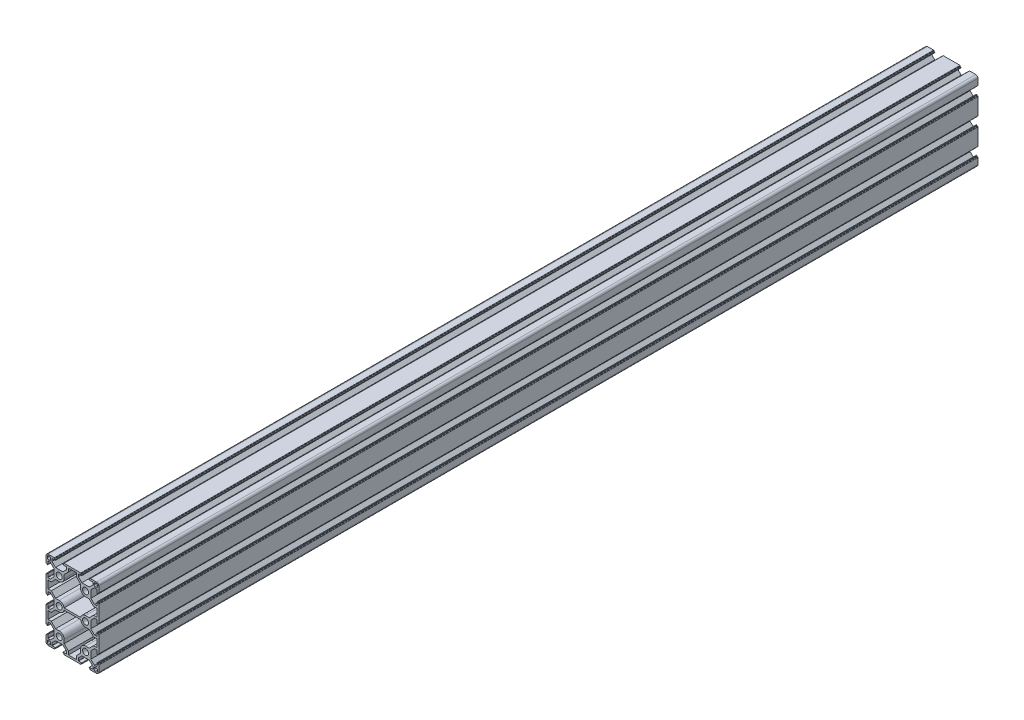
SolidWorks part; units mm, degrees
material "6063 T5"
ref_plane "Спереди" through (0, 0, 0) normal (0, 0, 1) x (1, 0, 0)
ref_plane "Сверху" through (0, 0, 0) normal (0, 1, 0) x (1, 0, 0)
ref_plane "Справа" through (0, 0, 0) normal (1, 0, 0) x (0, 0, -1)
sketch "Эскиз1" plane through (0, 0, 0) normal (0, 0, 1) x (1, 0, 0)
  line L0 (-34.4622, 45.0307) -> (-34.4622, -44.9693) construction
  line L1 (0, 45) -> (0, -45) construction
  line L2 (30, 0) -> (-30, 0) construction
  line L3 (-30, 38.25) -> (-30, 42.5)
  line L4 (-27.5, 45) -> (-23.25, 45)
  line L5 (4.5, 42.8) -> (-4.5, 42.8)
  line L6 (-27.35, 43.55) -> (-25.95, 43.55)
  line L7 (-28.55, 42.35) -> (-28.55, 40.95)
  line L8 (-27.35, 39.75) -> (-25.95, 39.75)
  line L9 (-24.75, 42.35) -> (-24.75, 40.95)
  line L10 (-4.5, 42.8) -> (-4.5, 38.9059)
  line L11 (-4.5, 38.9059) -> (-9.3, 34.1059)
  line L12 (-9.3, 34.1059) -> (-9.3, 30)
  line L13 (-15, 24.3) -> (-19.1059, 24.3)
  line L14 (-19.1059, 24.3) -> (-24.0559, 19.35)
  line L15 (-24.0559, 19.35) -> (-27.8, 19.35)
  line L16 (-27.8, 19.35) -> (-27.8, 10.65)
  line L17 (-27.8, 10.65) -> (-24.0559, 10.65)
  line L18 (-24.0559, 10.65) -> (-19.1059, 5.7)
  line L19 (-19.1059, 5.7) -> (-15, 5.7)
  line L20 (-9.4071, 1.1) -> (9.4071, 1.1)
  line L21 (-6.75, 45) -> (6.75, 45)
  line L22 (-30, 21.75) -> (-30, 8.25)
  line L23 (30, 21.75) -> (30, 8.25)
  line L24 (27.5, 45) -> (23.25, 45)
  line L25 (30, 38.25) -> (30, 42.5)
  line L26 (19.1059, 5.7) -> (15, 5.7)
  line L27 (24.0559, 10.65) -> (19.1059, 5.7)
  line L28 (27.8, 10.65) -> (24.0559, 10.65)
  line L29 (27.8, 19.35) -> (27.8, 10.65)
  line L30 (24.0559, 19.35) -> (27.8, 19.35)
  line L31 (19.1059, 24.3) -> (24.0559, 19.35)
  line L32 (15, 24.3) -> (19.1059, 24.3)
  line L33 (9.3, 34.1059) -> (9.3, 30)
  line L34 (4.5, 38.9059) -> (9.3, 34.1059)
  line L35 (4.5, 42.8) -> (4.5, 38.9059)
  line L36 (27.35, 43.55) -> (25.95, 43.55)
  line L37 (28.55, 42.35) -> (28.55, 40.95)
  line L38 (27.35, 39.75) -> (25.95, 39.75)
  line L39 (24.75, 42.35) -> (24.75, 40.95)
  line L40 (27.5, -45) -> (23.25, -45)
  line L41 (30, -38.25) -> (30, -42.5)
  line L42 (27.35, -43.55) -> (25.95, -43.55)
  line L43 (24.75, -42.35) -> (24.75, -40.95)
  line L44 (27.35, -39.75) -> (25.95, -39.75)
  line L45 (28.55, -42.35) -> (28.55, -40.95)
  line L46 (30, -21.75) -> (30, -8.25)
  line L47 (-30, -21.75) -> (-30, -8.25)
  line L48 (-6.75, -45) -> (6.75, -45)
  line L49 (-4.5, -42.8) -> (-4.5, -38.9059)
  line L50 (4.5, -42.8) -> (-4.5, -42.8)
  line L51 (4.5, -42.8) -> (4.5, -38.9059)
  line L52 (4.5, -38.9059) -> (9.3, -34.1059)
  line L53 (9.3, -34.1059) -> (9.3, -30)
  line L54 (15, -24.3) -> (19.1059, -24.3)
  line L55 (19.1059, -24.3) -> (24.0559, -19.35)
  line L56 (24.0559, -19.35) -> (27.8, -19.35)
  line L57 (27.8, -19.35) -> (27.8, -10.65)
  line L58 (27.8, -10.65) -> (24.0559, -10.65)
  line L59 (24.0559, -10.65) -> (19.1059, -5.7)
  line L60 (19.1059, -5.7) -> (15, -5.7)
  line L61 (-9.4071, -1.1) -> (9.4071, -1.1)
  line L62 (-19.1059, -5.7) -> (-15, -5.7)
  line L63 (-24.0559, -10.65) -> (-19.1059, -5.7)
  line L64 (-27.8, -10.65) -> (-24.0559, -10.65)
  line L65 (-27.8, -19.35) -> (-27.8, -10.65)
  line L66 (-24.0559, -19.35) -> (-27.8, -19.35)
  line L67 (-19.1059, -24.3) -> (-24.0559, -19.35)
  line L68 (-15, -24.3) -> (-19.1059, -24.3)
  line L69 (-9.3, -34.1059) -> (-9.3, -30)
  line L70 (-4.5, -38.9059) -> (-9.3, -34.1059)
  line L71 (-27.35, -43.55) -> (-25.95, -43.55)
  line L72 (-28.55, -42.35) -> (-28.55, -40.95)
  line L73 (-27.35, -39.75) -> (-25.95, -39.75)
  line L74 (-24.75, -42.35) -> (-24.75, -40.95)
  line L75 (-27.5, -45) -> (-23.25, -45)
  line L76 (-30, -38.25) -> (-30, -42.5)
  arc A0 (-30, 42.5) -> (-27.5, 45) centre (-27.5, 42.5) cw
  arc A1 (-28.55, 40.95) -> (-27.35, 39.75) centre (-27.35, 40.95) ccw
  arc A2 (-25.95, 39.75) -> (-24.75, 40.95) centre (-25.95, 40.95) ccw
  arc A3 (-25.95, 43.55) -> (-24.75, 42.35) centre (-25.95, 42.35) cw
  arc A4 (-27.35, 43.55) -> (-28.55, 42.35) centre (-27.35, 42.35) ccw
  circle A5 centre (-15, 30) radius 3.4
  arc A6 (-9.3, 30) -> (-15, 24.3) centre (-15, 30) cw
  arc A7 (-15, 5.7) -> (-9.4071, 1.1) centre (-15, 0) cw
  circle A8 centre (-15, 0) radius 3.4
  arc A9 (30, 42.5) -> (27.5, 45) centre (27.5, 42.5) ccw
  arc A10 (15, 5.7) -> (9.4071, 1.1) centre (15, 0) ccw
  arc A11 (9.3, 30) -> (15, 24.3) centre (15, 30) ccw
  circle A12 centre (15, 30) radius 3.4
  circle A13 centre (15, 0) radius 3.4
  arc A14 (25.95, 43.55) -> (24.75, 42.35) centre (25.95, 42.35) ccw
  arc A15 (27.35, 43.55) -> (28.55, 42.35) centre (27.35, 42.35) cw
  arc A16 (28.55, 40.95) -> (27.35, 39.75) centre (27.35, 40.95) cw
  arc A17 (25.95, 39.75) -> (24.75, 40.95) centre (25.95, 40.95) cw
  arc A18 (30, -42.5) -> (27.5, -45) centre (27.5, -42.5) cw
  arc A19 (27.35, -43.55) -> (28.55, -42.35) centre (27.35, -42.35) ccw
  arc A20 (25.95, -43.55) -> (24.75, -42.35) centre (25.95, -42.35) cw
  arc A21 (25.95, -39.75) -> (24.75, -40.95) centre (25.95, -40.95) ccw
  arc A22 (28.55, -40.95) -> (27.35, -39.75) centre (27.35, -40.95) ccw
  circle A23 centre (-15, -30) radius 3.4
  circle A24 centre (15, -30) radius 3.4
  arc A25 (9.3, -30) -> (15, -24.3) centre (15, -30) cw
  arc A26 (15, -5.7) -> (9.4071, -1.1) centre (15, 0) cw
  arc A27 (-15, -5.7) -> (-9.4071, -1.1) centre (-15, 0) ccw
  arc A28 (-9.3, -30) -> (-15, -24.3) centre (-15, -30) ccw
  arc A29 (-25.95, -43.55) -> (-24.75, -42.35) centre (-25.95, -42.35) ccw
  arc A30 (-27.35, -43.55) -> (-28.55, -42.35) centre (-27.35, -42.35) cw
  arc A31 (-28.55, -40.95) -> (-27.35, -39.75) centre (-27.35, -40.95) cw
  arc A32 (-25.95, -39.75) -> (-24.75, -40.95) centre (-25.95, -40.95) cw
  arc A33 (-30, -42.5) -> (-27.5, -45) centre (-27.5, -42.5) ccw
  point P22 (-24.75, 43.55)
  point P25 (-28.55, 43.55)
  point P63 (0, 1.1)
  point P72 (0, 42.8)
  line B0 (-30, 8.25) -> (-30, 5.5)
  line B1 (-29.7, 5.2) -> (-29.3, 5.2)
  line B2 (-29, 4.9) -> (-29, 4.4)
  line B3 (-28.7, 4.1) -> (-28.3, 4.1)
  line B4 (-28, 4.4) -> (-28, 7.95)
  line B5 (-27.7, 8.25) -> (-25.05, 8.25)
  line B6 (-25.05, 8.25) -> (-21, 4.2)
  line B7 (-21, 0) -> (-30, 0) construction
  line B8 (-21, -4.2) -> (-21, 4.2)
  line B9 (-25.05, -8.25) -> (-21, -4.2)
  line B10 (-27.7, -8.25) -> (-25.05, -8.25)
  line B11 (-28, -4.4) -> (-28, -7.95)
  line B12 (-28.7, -4.1) -> (-28.3, -4.1)
  line B13 (-29, -4.9) -> (-29, -4.4)
  line B14 (-29.7, -5.2) -> (-29.3, -5.2)
  line B15 (-30, -8.25) -> (-30, -5.5)
  arc B16 (-28, 7.95) -> (-27.7, 8.25) centre (-27.7, 7.95) cw
  arc B17 (-28.3, 4.1) -> (-28, 4.4) centre (-28.3, 4.4) ccw
  arc B18 (-29, 4.4) -> (-28.7, 4.1) centre (-28.7, 4.4) ccw
  arc B19 (-29.3, 5.2) -> (-29, 4.9) centre (-29.3, 4.9) cw
  arc B20 (-30, 5.5) -> (-29.7, 5.2) centre (-29.7, 5.5) ccw
  arc B21 (-30, -5.5) -> (-29.7, -5.2) centre (-29.7, -5.5) cw
  arc B22 (-29.3, -5.2) -> (-29, -4.9) centre (-29.3, -4.9) ccw
  arc B23 (-29, -4.4) -> (-28.7, -4.1) centre (-28.7, -4.4) cw
  arc B24 (-28.3, -4.1) -> (-28, -4.4) centre (-28.3, -4.4) cw
  arc B25 (-28, -7.95) -> (-27.7, -8.25) centre (-27.7, -7.95) ccw
  line B26 (-30, 38.25) -> (-30, 35.5)
  line B27 (-29.7, 35.2) -> (-29.3, 35.2)
  line B28 (-29, 34.9) -> (-29, 34.4)
  line B29 (-28.7, 34.1) -> (-28.3, 34.1)
  line B30 (-28, 34.4) -> (-28, 37.95)
  line B31 (-27.7, 38.25) -> (-25.05, 38.25)
  line B32 (-25.05, 38.25) -> (-21, 34.2)
  line B33 (-21, 30) -> (-30, 30) construction
  line B34 (-21, 25.8) -> (-21, 34.2)
  line B35 (-25.05, 21.75) -> (-21, 25.8)
  line B36 (-27.7, 21.75) -> (-25.05, 21.75)
  line B37 (-28, 25.6) -> (-28, 22.05)
  line B38 (-28.7, 25.9) -> (-28.3, 25.9)
  line B39 (-29, 25.1) -> (-29, 25.6)
  line B40 (-29.7, 24.8) -> (-29.3, 24.8)
  line B41 (-30, 21.75) -> (-30, 24.5)
  arc B42 (-28, 37.95) -> (-27.7, 38.25) centre (-27.7, 37.95) cw
  arc B43 (-28.3, 34.1) -> (-28, 34.4) centre (-28.3, 34.4) ccw
  arc B44 (-29, 34.4) -> (-28.7, 34.1) centre (-28.7, 34.4) ccw
  arc B45 (-29.3, 35.2) -> (-29, 34.9) centre (-29.3, 34.9) cw
  arc B46 (-30, 35.5) -> (-29.7, 35.2) centre (-29.7, 35.5) ccw
  arc B47 (-30, 24.5) -> (-29.7, 24.8) centre (-29.7, 24.5) cw
  arc B48 (-29.3, 24.8) -> (-29, 25.1) centre (-29.3, 25.1) ccw
  arc B49 (-29, 25.6) -> (-28.7, 25.9) centre (-28.7, 25.6) cw
  arc B50 (-28.3, 25.9) -> (-28, 25.6) centre (-28.3, 25.6) cw
  arc B51 (-28, 22.05) -> (-27.7, 21.75) centre (-27.7, 22.05) ccw
  line B52 (-6.75, 45) -> (-9.5, 45)
  line B53 (-9.8, 44.7) -> (-9.8, 44.3)
  line B54 (-10.1, 44) -> (-10.6, 44)
  line B55 (-10.9, 43.7) -> (-10.9, 43.3)
  line B56 (-10.6, 43) -> (-7.05, 43)
  line B57 (-6.75, 42.7) -> (-6.75, 40.05)
  line B58 (-6.75, 40.05) -> (-10.8, 36)
  line B59 (-15, 36) -> (-15, 45) construction
  line B60 (-19.2, 36) -> (-10.8, 36)
  line B61 (-23.25, 40.05) -> (-19.2, 36)
  line B62 (-23.25, 42.7) -> (-23.25, 40.05)
  line B63 (-19.4, 43) -> (-22.95, 43)
  line B64 (-19.1, 43.7) -> (-19.1, 43.3)
  line B65 (-19.9, 44) -> (-19.4, 44)
  line B66 (-20.2, 44.7) -> (-20.2, 44.3)
  line B67 (-23.25, 45) -> (-20.5, 45)
  arc B68 (-7.05, 43) -> (-6.75, 42.7) centre (-7.05, 42.7) cw
  arc B69 (-10.9, 43.3) -> (-10.6, 43) centre (-10.6, 43.3) ccw
  arc B70 (-10.6, 44) -> (-10.9, 43.7) centre (-10.6, 43.7) ccw
  arc B71 (-9.8, 44.3) -> (-10.1, 44) centre (-10.1, 44.3) cw
  arc B72 (-9.5, 45) -> (-9.8, 44.7) centre (-9.5, 44.7) ccw
  arc B73 (-20.5, 45) -> (-20.2, 44.7) centre (-20.5, 44.7) cw
  arc B74 (-20.2, 44.3) -> (-19.9, 44) centre (-19.9, 44.3) ccw
  arc B75 (-19.4, 44) -> (-19.1, 43.7) centre (-19.4, 43.7) cw
  arc B76 (-19.1, 43.3) -> (-19.4, 43) centre (-19.4, 43.3) cw
  arc B77 (-22.95, 43) -> (-23.25, 42.7) centre (-22.95, 42.7) ccw
  line B78 (6.75, 45) -> (9.5, 45)
  line B79 (9.8, 44.7) -> (9.8, 44.3)
  line B80 (10.1, 44) -> (10.6, 44)
  line B81 (10.9, 43.7) -> (10.9, 43.3)
  line B82 (10.6, 43) -> (7.05, 43)
  line B83 (6.75, 42.7) -> (6.75, 40.05)
  line B84 (6.75, 40.05) -> (10.8, 36)
  line B85 (15, 36) -> (15, 45) construction
  line B86 (19.2, 36) -> (10.8, 36)
  line B87 (23.25, 40.05) -> (19.2, 36)
  line B88 (23.25, 42.7) -> (23.25, 40.05)
  line B89 (19.4, 43) -> (22.95, 43)
  line B90 (19.1, 43.7) -> (19.1, 43.3)
  line B91 (19.9, 44) -> (19.4, 44)
  line B92 (20.2, 44.7) -> (20.2, 44.3)
  line B93 (23.25, 45) -> (20.5, 45)
  arc B94 (7.05, 43) -> (6.75, 42.7) centre (7.05, 42.7) ccw
  arc B95 (10.9, 43.3) -> (10.6, 43) centre (10.6, 43.3) cw
  arc B96 (10.6, 44) -> (10.9, 43.7) centre (10.6, 43.7) cw
  arc B97 (9.8, 44.3) -> (10.1, 44) centre (10.1, 44.3) ccw
  arc B98 (9.5, 45) -> (9.8, 44.7) centre (9.5, 44.7) cw
  arc B99 (20.5, 45) -> (20.2, 44.7) centre (20.5, 44.7) ccw
  arc B100 (20.2, 44.3) -> (19.9, 44) centre (19.9, 44.3) cw
  arc B101 (19.4, 44) -> (19.1, 43.7) centre (19.4, 43.7) ccw
  arc B102 (19.1, 43.3) -> (19.4, 43) centre (19.4, 43.3) ccw
  arc B103 (22.95, 43) -> (23.25, 42.7) centre (22.95, 42.7) cw
  line B104 (30, 38.25) -> (30, 35.5)
  line B105 (29.7, 35.2) -> (29.3, 35.2)
  line B106 (29, 34.9) -> (29, 34.4)
  line B107 (28.7, 34.1) -> (28.3, 34.1)
  line B108 (28, 34.4) -> (28, 37.95)
  line B109 (27.7, 38.25) -> (25.05, 38.25)
  line B110 (25.05, 38.25) -> (21, 34.2)
  line B111 (21, 30) -> (30, 30) construction
  line B112 (21, 25.8) -> (21, 34.2)
  line B113 (25.05, 21.75) -> (21, 25.8)
  line B114 (27.7, 21.75) -> (25.05, 21.75)
  line B115 (28, 25.6) -> (28, 22.05)
  line B116 (28.7, 25.9) -> (28.3, 25.9)
  line B117 (29, 25.1) -> (29, 25.6)
  line B118 (29.7, 24.8) -> (29.3, 24.8)
  line B119 (30, 21.75) -> (30, 24.5)
  arc B120 (28, 37.95) -> (27.7, 38.25) centre (27.7, 37.95) ccw
  arc B121 (28.3, 34.1) -> (28, 34.4) centre (28.3, 34.4) cw
  arc B122 (29, 34.4) -> (28.7, 34.1) centre (28.7, 34.4) cw
  arc B123 (29.3, 35.2) -> (29, 34.9) centre (29.3, 34.9) ccw
  arc B124 (30, 35.5) -> (29.7, 35.2) centre (29.7, 35.5) cw
  arc B125 (30, 24.5) -> (29.7, 24.8) centre (29.7, 24.5) ccw
  arc B126 (29.3, 24.8) -> (29, 25.1) centre (29.3, 25.1) cw
  arc B127 (29, 25.6) -> (28.7, 25.9) centre (28.7, 25.6) ccw
  arc B128 (28.3, 25.9) -> (28, 25.6) centre (28.3, 25.6) ccw
  arc B129 (28, 22.05) -> (27.7, 21.75) centre (27.7, 22.05) cw
  line B130 (30, 8.25) -> (30, 5.5)
  line B131 (29.7, 5.2) -> (29.3, 5.2)
  line B132 (29, 4.9) -> (29, 4.4)
  line B133 (28.7, 4.1) -> (28.3, 4.1)
  line B134 (28, 4.4) -> (28, 7.95)
  line B135 (27.7, 8.25) -> (25.05, 8.25)
  line B136 (25.05, 8.25) -> (21, 4.2)
  line B137 (21, 0) -> (30, 0) construction
  line B138 (21, -4.2) -> (21, 4.2)
  line B139 (25.05, -8.25) -> (21, -4.2)
  line B140 (27.7, -8.25) -> (25.05, -8.25)
  line B141 (28, -4.4) -> (28, -7.95)
  line B142 (28.7, -4.1) -> (28.3, -4.1)
  line B143 (29, -4.9) -> (29, -4.4)
  line B144 (29.7, -5.2) -> (29.3, -5.2)
  line B145 (30, -8.25) -> (30, -5.5)
  arc B146 (28, 7.95) -> (27.7, 8.25) centre (27.7, 7.95) ccw
  arc B147 (28.3, 4.1) -> (28, 4.4) centre (28.3, 4.4) cw
  arc B148 (29, 4.4) -> (28.7, 4.1) centre (28.7, 4.4) cw
  arc B149 (29.3, 5.2) -> (29, 4.9) centre (29.3, 4.9) ccw
  arc B150 (30, 5.5) -> (29.7, 5.2) centre (29.7, 5.5) cw
  arc B151 (30, -5.5) -> (29.7, -5.2) centre (29.7, -5.5) ccw
  arc B152 (29.3, -5.2) -> (29, -4.9) centre (29.3, -4.9) cw
  arc B153 (29, -4.4) -> (28.7, -4.1) centre (28.7, -4.4) ccw
  arc B154 (28.3, -4.1) -> (28, -4.4) centre (28.3, -4.4) ccw
  arc B155 (28, -7.95) -> (27.7, -8.25) centre (27.7, -7.95) cw
  line B156 (-6.75, -45) -> (-9.5, -45)
  line B157 (-9.8, -44.7) -> (-9.8, -44.3)
  line B158 (-10.1, -44) -> (-10.6, -44)
  line B159 (-10.9, -43.7) -> (-10.9, -43.3)
  line B160 (-10.6, -43) -> (-7.05, -43)
  line B161 (-6.75, -42.7) -> (-6.75, -40.05)
  line B162 (-6.75, -40.05) -> (-10.8, -36)
  line B163 (-15, -36) -> (-15, -45) construction
  line B164 (-19.2, -36) -> (-10.8, -36)
  line B165 (-23.25, -40.05) -> (-19.2, -36)
  line B166 (-23.25, -42.7) -> (-23.25, -40.05)
  line B167 (-19.4, -43) -> (-22.95, -43)
  line B168 (-19.1, -43.7) -> (-19.1, -43.3)
  line B169 (-19.9, -44) -> (-19.4, -44)
  line B170 (-20.2, -44.7) -> (-20.2, -44.3)
  line B171 (-23.25, -45) -> (-20.5, -45)
  arc B172 (-7.05, -43) -> (-6.75, -42.7) centre (-7.05, -42.7) ccw
  arc B173 (-10.9, -43.3) -> (-10.6, -43) centre (-10.6, -43.3) cw
  arc B174 (-10.6, -44) -> (-10.9, -43.7) centre (-10.6, -43.7) cw
  arc B175 (-9.8, -44.3) -> (-10.1, -44) centre (-10.1, -44.3) ccw
  arc B176 (-9.5, -45) -> (-9.8, -44.7) centre (-9.5, -44.7) cw
  arc B177 (-20.5, -45) -> (-20.2, -44.7) centre (-20.5, -44.7) ccw
  arc B178 (-20.2, -44.3) -> (-19.9, -44) centre (-19.9, -44.3) cw
  arc B179 (-19.4, -44) -> (-19.1, -43.7) centre (-19.4, -43.7) ccw
  arc B180 (-19.1, -43.3) -> (-19.4, -43) centre (-19.4, -43.3) ccw
  arc B181 (-22.95, -43) -> (-23.25, -42.7) centre (-22.95, -42.7) cw
  line B182 (-30, -38.25) -> (-30, -35.5)
  line B183 (-29.7, -35.2) -> (-29.3, -35.2)
  line B184 (-29, -34.9) -> (-29, -34.4)
  line B185 (-28.7, -34.1) -> (-28.3, -34.1)
  line B186 (-28, -34.4) -> (-28, -37.95)
  line B187 (-27.7, -38.25) -> (-25.05, -38.25)
  line B188 (-25.05, -38.25) -> (-21, -34.2)
  line B189 (-21, -30) -> (-30, -30) construction
  line B190 (-21, -25.8) -> (-21, -34.2)
  line B191 (-25.05, -21.75) -> (-21, -25.8)
  line B192 (-27.7, -21.75) -> (-25.05, -21.75)
  line B193 (-28, -25.6) -> (-28, -22.05)
  line B194 (-28.7, -25.9) -> (-28.3, -25.9)
  line B195 (-29, -25.1) -> (-29, -25.6)
  line B196 (-29.7, -24.8) -> (-29.3, -24.8)
  line B197 (-30, -21.75) -> (-30, -24.5)
  arc B198 (-28, -37.95) -> (-27.7, -38.25) centre (-27.7, -37.95) ccw
  arc B199 (-28.3, -34.1) -> (-28, -34.4) centre (-28.3, -34.4) cw
  arc B200 (-29, -34.4) -> (-28.7, -34.1) centre (-28.7, -34.4) cw
  arc B201 (-29.3, -35.2) -> (-29, -34.9) centre (-29.3, -34.9) ccw
  arc B202 (-30, -35.5) -> (-29.7, -35.2) centre (-29.7, -35.5) cw
  arc B203 (-30, -24.5) -> (-29.7, -24.8) centre (-29.7, -24.5) ccw
  arc B204 (-29.3, -24.8) -> (-29, -25.1) centre (-29.3, -25.1) cw
  arc B205 (-29, -25.6) -> (-28.7, -25.9) centre (-28.7, -25.6) ccw
  arc B206 (-28.3, -25.9) -> (-28, -25.6) centre (-28.3, -25.6) ccw
  arc B207 (-28, -22.05) -> (-27.7, -21.75) centre (-27.7, -22.05) cw
  line B208 (30, -38.25) -> (30, -35.5)
  line B209 (29.7, -35.2) -> (29.3, -35.2)
  line B210 (29, -34.9) -> (29, -34.4)
  line B211 (28.7, -34.1) -> (28.3, -34.1)
  line B212 (28, -34.4) -> (28, -37.95)
  line B213 (27.7, -38.25) -> (25.05, -38.25)
  line B214 (25.05, -38.25) -> (21, -34.2)
  line B215 (21, -30) -> (30, -30) construction
  line B216 (21, -25.8) -> (21, -34.2)
  line B217 (25.05, -21.75) -> (21, -25.8)
  line B218 (27.7, -21.75) -> (25.05, -21.75)
  line B219 (28, -25.6) -> (28, -22.05)
  line B220 (28.7, -25.9) -> (28.3, -25.9)
  line B221 (29, -25.1) -> (29, -25.6)
  line B222 (29.7, -24.8) -> (29.3, -24.8)
  line B223 (30, -21.75) -> (30, -24.5)
  arc B224 (28, -37.95) -> (27.7, -38.25) centre (27.7, -37.95) cw
  arc B225 (28.3, -34.1) -> (28, -34.4) centre (28.3, -34.4) ccw
  arc B226 (29, -34.4) -> (28.7, -34.1) centre (28.7, -34.4) ccw
  arc B227 (29.3, -35.2) -> (29, -34.9) centre (29.3, -34.9) cw
  arc B228 (30, -35.5) -> (29.7, -35.2) centre (29.7, -35.5) ccw
  arc B229 (30, -24.5) -> (29.7, -24.8) centre (29.7, -24.5) cw
  arc B230 (29.3, -24.8) -> (29, -25.1) centre (29.3, -25.1) ccw
  arc B231 (29, -25.6) -> (28.7, -25.9) centre (28.7, -25.6) cw
  arc B232 (28.3, -25.9) -> (28, -25.6) centre (28.3, -25.6) cw
  arc B233 (28, -22.05) -> (27.7, -21.75) centre (27.7, -22.05) ccw
  line B234 (6.75, -45) -> (9.5, -45)
  line B235 (9.8, -44.7) -> (9.8, -44.3)
  line B236 (10.1, -44) -> (10.6, -44)
  line B237 (10.9, -43.7) -> (10.9, -43.3)
  line B238 (10.6, -43) -> (7.05, -43)
  line B239 (6.75, -42.7) -> (6.75, -40.05)
  line B240 (6.75, -40.05) -> (10.8, -36)
  line B241 (15, -36) -> (15, -45) construction
  line B242 (19.2, -36) -> (10.8, -36)
  line B243 (23.25, -40.05) -> (19.2, -36)
  line B244 (23.25, -42.7) -> (23.25, -40.05)
  line B245 (19.4, -43) -> (22.95, -43)
  line B246 (19.1, -43.7) -> (19.1, -43.3)
  line B247 (19.9, -44) -> (19.4, -44)
  line B248 (20.2, -44.7) -> (20.2, -44.3)
  line B249 (23.25, -45) -> (20.5, -45)
  arc B250 (7.05, -43) -> (6.75, -42.7) centre (7.05, -42.7) cw
  arc B251 (10.9, -43.3) -> (10.6, -43) centre (10.6, -43.3) ccw
  arc B252 (10.6, -44) -> (10.9, -43.7) centre (10.6, -43.7) ccw
  arc B253 (9.8, -44.3) -> (10.1, -44) centre (10.1, -44.3) cw
  arc B254 (9.5, -45) -> (9.8, -44.7) centre (9.5, -44.7) ccw
  arc B255 (20.5, -45) -> (20.2, -44.7) centre (20.5, -44.7) cw
  arc B256 (20.2, -44.3) -> (19.9, -44) centre (19.9, -44.3) ccw
  arc B257 (19.4, -44) -> (19.1, -43.7) centre (19.4, -43.7) cw
  arc B258 (19.1, -43.3) -> (19.4, -43) centre (19.4, -43.3) cw
  arc B259 (22.95, -43) -> (23.25, -42.7) centre (22.95, -42.7) ccw
  dimension "D6" = 2.5
  dimension "D10" = 1.2
  dimension "D11" = 6.8
  dimension "D17" = 5.7
  dimension "D1" = 90
  dimension "D2" = 90
  dimension "D3" = 60
  dimension "D4" = 30
  dimension "D5" = 15
  dimension "D7" = 1.5
  dimension "D8" = 1.5
  dimension "D9" = 3.8
  dimension "D12" = 2.2
  dimension "D13" = 4.5
  dimension "D14" = 2.4
  dimension "D15" = 2.4
  dimension "D16" = 2.4
  dimension "D18" = 2.2
  dimension "D19" = 2.4
  dimension "D20" = 2.4
  dimension "D21" = 1.1
sketch_block_instance "8B(16,5P_low)-1"
sketch_block "8B(16,5P_low)" parameters "D6"=0.3, "D1"=16.5, "D2"=8.4, "D3"=9, "D4"=45, "D5"=10.4, "D7"=2, "D8"=1, "D9"=8.2, "D10"=8.4
sketch_block_instance "8B(16,5P_low)-3"
sketch_block_instance "8B(16,5P_low)-4"
sketch_block_instance "8B(16,5P_low)-5"
sketch_block_instance "8B(16,5P_low)-6"
sketch_block_instance "8B(16,5P_low)-7"
sketch_block_instance "8B(16,5P_low)-20"
sketch_block_instance "8B(16,5P_low)-21"
sketch_block_instance "8B(16,5P_low)-22"
sketch_block_instance "8B(16,5P_low)-23"
extrude "Бобышка-Вытянуть1" add sketch "Эскиз1" along normal blind 1000 contours B259 B245 B258 B246 B257 B247 B256 B248 B255 B249 L40 A18 L41 B208 B228 B209 B227 B210 B226 B211 B225 B212 B224 B213 B214 B216 B217 B218 B233 B219 B232 B220 B231 B221 B230 B222 B229 B223 L46 B145 B151 B144 B152 B143 B153 B142 B154 B141 B155 B140 B139
